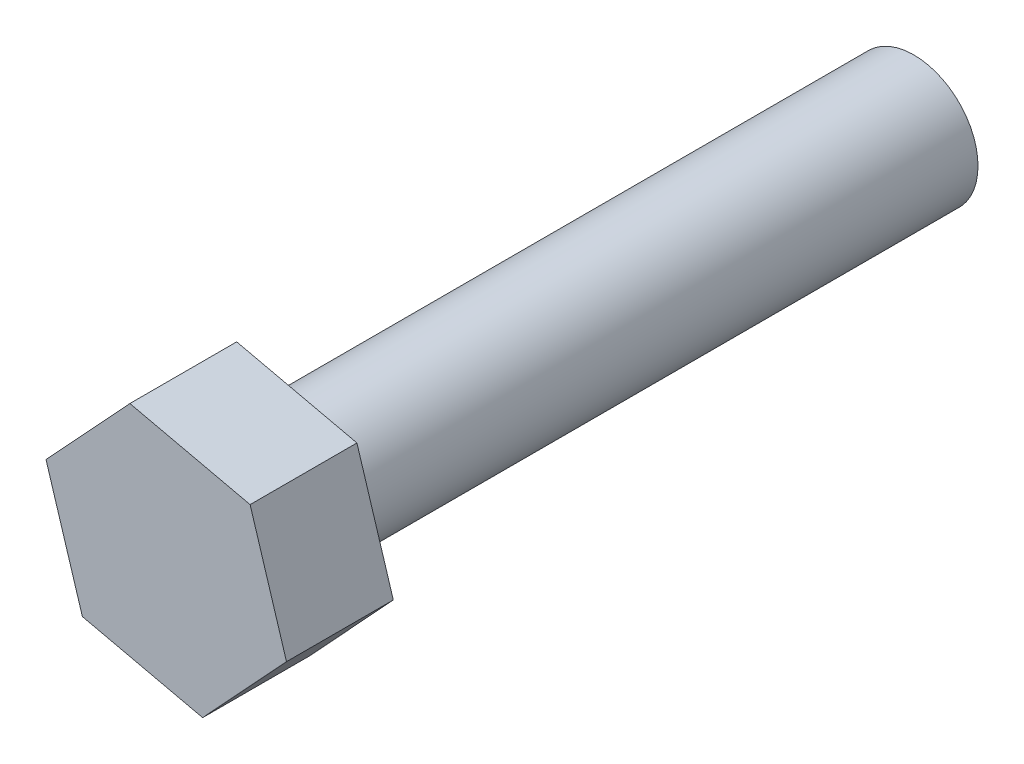
SolidWorks part; units mm, degrees
ref_plane "前视基准面" through (0, 0, 0) normal (0, 0, 1) x (1, 0, 0)
ref_plane "上视基准面" through (0, 0, 0) normal (0, 1, 0) x (1, 0, 0)
ref_plane "右视基准面" through (0, 0, 0) normal (1, 0, 0) x (0, 0, -1)
sketch "草图1" plane through (0, 0, 0) normal (0, 0, 1) x (1, 0, 0)
  circle A0 centre (0, 0) radius 3
  dimension "D1" = 6
extrude "凸台-拉伸1" add sketch "草图1" along normal blind 30
sketch "草图2" plane through (0, 0, 30) normal (0, 0, 1) x (1, 0, 0)
  line L1 (3.9259, 4.2332) -> (-1.7031, 5.5166)
  line L2 (-1.7031, 5.5166) -> (-5.6291, 1.2833)
  line L3 (-5.6291, 1.2833) -> (-3.9259, -4.2332)
  line L4 (-3.9259, -4.2332) -> (1.7031, -5.5166)
  line L5 (1.7031, -5.5166) -> (5.6291, -1.2833)
  line L6 (5.6291, -1.2833) -> (3.9259, 4.2332)
  circle A0 centre (0, 0) radius 5 construction
  dimension "D1" = 10
extrude "凸台-拉伸2" add sketch "草图2" along normal blind 5
